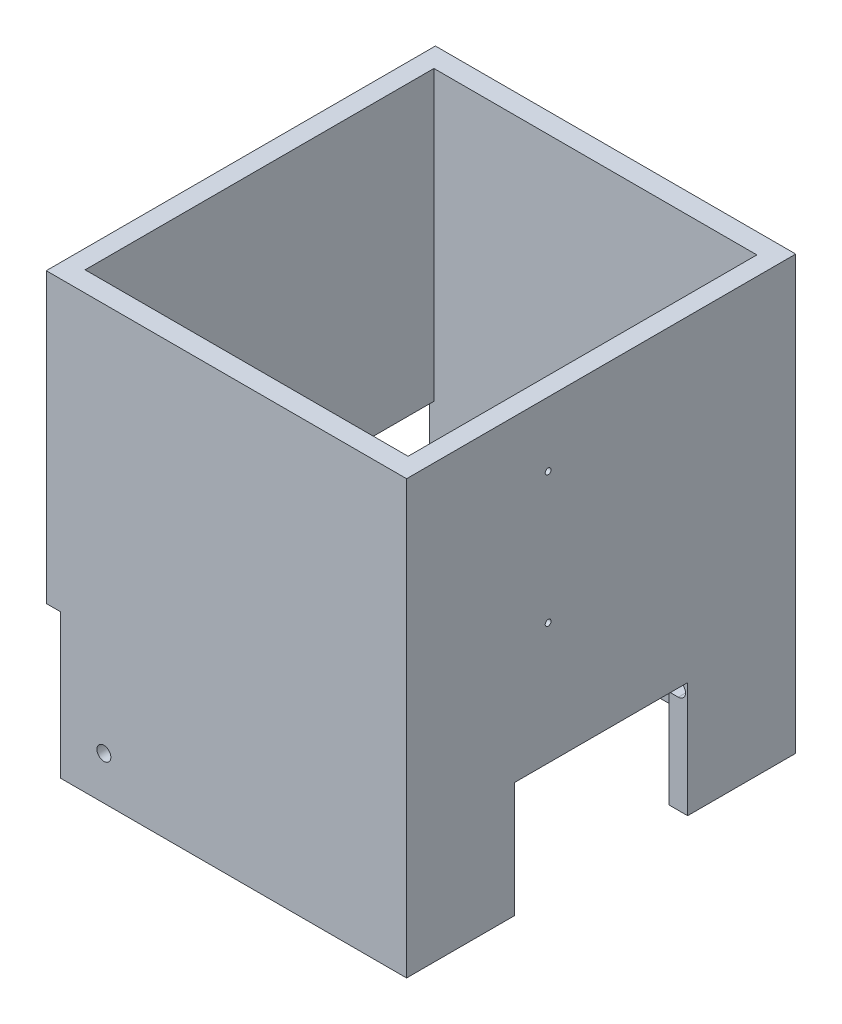
SolidWorks part; units mm, degrees
material "ABS"
ref_plane "Front" through (0, 0, 0) normal (0, 0, 1) x (1, 0, 0)
ref_plane "Top" through (0, 0, 0) normal (0, 1, 0) x (1, 0, 0)
ref_plane "Right" through (0, 0, 0) normal (1, 0, 0) x (0, 0, -1)
sketch "Sketch1" plane through (0, 0, 0) normal (0, 1, 0) x (1, 0, 0)
  line L1 (-62.5, 67.5) -> (62.5, 67.5)
  line L2 (-62.5, 67.5) -> (-62.5, -67.5)
  line L3 (-62.5, -67.5) -> (62.5, -67.5)
  line L4 (62.5, 67.5) -> (62.5, -67.5)
  line L5 (-62.5, 67.5) -> (62.5, -67.5) construction
  line L6 (-62.5, -67.5) -> (62.5, 67.5) construction
  line L7 (-56.0185, -60.5) -> (56.0185, -60.5)
  line L8 (-56.0185, -60.5) -> (-56.0185, 60.5)
  line L9 (-56.0185, 60.5) -> (56.0185, 60.5)
  line L10 (56.0185, -60.5) -> (56.0185, 60.5)
  line L11 (-56.0185, -60.5) -> (56.0185, 60.5) construction
  line L12 (-56.0185, 60.5) -> (56.0185, -60.5) construction
  point P0 (0, 0)
  point P6 (0, 0)
  point P11 (0, 0)
  dimension "D1" = 125
  dimension "D2" = 135
  dimension "D3" = 121
extrude "Boss-Extrude1" add sketch "Sketch1" along normal blind 150
sketch "Sketch3" plane through (0, 0, 0) normal (0, 0, 1) x (1, 0, 0)
  line L1 (-62.5, 0) -> (-57.5, 0)
  line L2 (-62.5, 0) -> (-62.5, 50)
  line L3 (-62.5, 50) -> (-57.5, 50)
  line L4 (-57.5, 0) -> (-57.5, 50)
  dimension "D1" = 5
  dimension "D2" = 50
extrude "Cut-Extrude1" cut sketch "Sketch3" against normal through all and the other way through all
sketch "Sketch4" plane through (62.5, 0, 0) normal (1, 0, 0) x (0, 0, -1)
  line L0 (-67.5, 0) -> (67.5, 0) construction
  line L1 (-30, 0) -> (30, 0)
  line L2 (-30, 0) -> (-30, 40)
  line L3 (-30, 40) -> (30, 40)
  line L4 (30, 0) -> (30, 40)
  point P6 (0, 0)
  dimension "D1" = 40
  dimension "D2" = 60
extrude "Cut-Extrude2" cut sketch "Sketch4" against normal up to next
sketch "Sketch9" plane through (0, 0, 67.5) normal (0, 0, 1) x (1, 0, 0)
  circle A0 centre (-42.5, 15) radius 2.413 construction
  point P0 (-42.5, 15)
hole_wizard "#10 Clearance Hole1" positions "Sketch10" profile "Sketch11" hole size "#10" standard "ANSI Inch"
sketch "Sketch10" plane through (0, 0, 67.5) normal (0, 0, 1) x (1, 0, 0)
  point P0 (-42.5, 15)
sketch "Sketch11" plane through (-42.5, 15, 67.5) normal (1, 0, 0) x (0, -1, 0)
  line L0 (0, 0) -> (0, 26.8499)
  line L1 (0, 26.8499) -> (2.413, 25.4)
  line L2 (2.413, 25.4) -> (2.413, 0)
  line L5 (2.413, 0) -> (0, 0)
  line L10 (0, 26.8499) -> (-2.413, 25.4) construction
  line L11 (0, -6.35) -> (0, 107.95) construction
  dimension "Hole Dia." = 4.826
  dimension "Hole Depth" = 25.4
  dimension "Drill Angle" = 118
mirror "Mirror1" about plane through (0, 0, 0) normal (0, 0, 1) of "#10 Clearance Hole1"
sketch "Sketch12" plane through (0, 0, 0) normal (0, 0, 1) x (1, 0, 0)
  line L0 (56.0185, 39) -> (56.0185, 34)
  line L1 (56.0185, 0) -> (56.0185, 40) construction
  line L2 (56.0185, 150) -> (56.0185, 0) construction
  line L3 (56.0185, 34) -> (59.2593, 34)
  line L4 (56.0185, 39) -> (59.2593, 39)
  line L5 (56.0185, 0) -> (62.5, 0) construction
  line L6 (56.0185, 40) -> (62.5, 40) construction
  arc A0 (59.2593, 39) -> (59.2593, 34) centre (59.2593, 36.5) cw
  point P11 (59.2593, 0)
  dimension "D1" = 2.5
  dimension "D2" = 1
extrude "Cut-Extrude3" cut sketch "Sketch12" against normal mid plane 75
hole_wizard "#2 Clearance Hole1" positions "Sketch15" profile "Sketch16" hole size "#2" standard "ANSI Inch" end condition up to next
sketch "Sketch15" plane through (62.5, 0, 0) normal (1, 0, 0) x (0, 0, -1)
  point P0 (-18.3915, 127.6569)
  point P3 (-18.3915, 82.1569)
sketch "Sketch16" plane through (62.5, 127.6569, 18.3915) normal (0, 1, 0) x (0, 0, -1)
  line L0 (0, 0) -> (0, 6.4815)
  line L1 (0, 6.4815) -> (1.016, 6.4815)
  line L2 (1.016, 6.4815) -> (1.016, 0)
  line L5 (1.016, 0) -> (0, 0)
  line L11 (0, -6.35) -> (0, 107.95) construction
  dimension "Thru Hole Dia." = 2.032
  dimension "Thru Hole Depth" = 6.4815
hole_wizard "#3 Clearance Hole1" positions "Sketch17" profile "Sketch18" hole size "#3" standard "ANSI Inch"
sketch "Sketch17" plane through (-56.0185, 0, 0) normal (1, 0, 0) x (0, 0, -1)
  point P0 (10.2126, 67.1121)
  point P3 (18.7126, 67.1121)
sketch "Sketch18" plane through (-56.0185, 67.1121, -10.2126) normal (0, 1, 0) x (0, 0, -1)
  line L0 (0, 0) -> (0, 3.9381)
  line L1 (0, 3.9381) -> (1.27, 3.175)
  line L2 (1.27, 3.175) -> (1.27, 0.6858)
  line L3 (1.27, 0.6858) -> (1.9558, 0)
  line L5 (1.9558, 0) -> (0, 0)
  line L6 (-1.27, 0.6858) -> (-1.9558, 0) construction
  line L10 (0, 3.9381) -> (-1.27, 3.175) construction
  line L11 (0, -6.35) -> (0, 107.95) construction
  dimension "Hole Dia." = 2.54
  dimension "Hole Depth" = 3.175
  dimension "Near C'Sink Dia." = 3.9116
  dimension "Near C'Sink Angle" = 90
  dimension "Drill Angle" = 118
sketch "Sketch19" plane through (-57.5, 0, 0) normal (-1, 0, 0) x (0, 0, 1)
  line L0 (-67.5, 0) -> (67.5, 0) construction
  line L1 (-60.5, 0) -> (60.5, 0)
  line L2 (-60.5, 0) -> (-60.5, 50)
  line L3 (-60.5, 50) -> (60.5, 50)
  line L4 (60.5, 0) -> (60.5, 50)
  line L5 (-67.5, 50) -> (67.5, 50) construction
  line L6 (-67.5, 0) -> (-67.5, 50) construction
  line L7 (67.5, 0) -> (67.5, 50) construction
  point P8 (0, 0)
  point P9 (0, 0)
  point P10 (60.0929, 0)
  point P11 (0, 0)
  dimension "D1" = 7
  dimension "D2" = 7
extrude "Cut-Extrude4" cut sketch "Sketch19" against normal up to next
